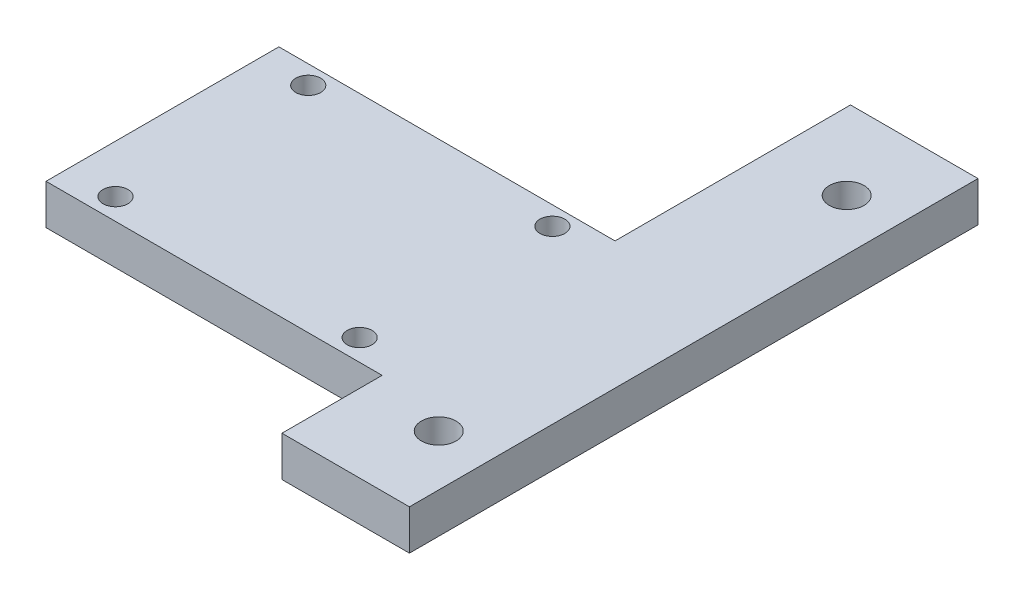
SolidWorks part; units mm, degrees
material "ABS"
ref_plane "Front Plane" through (0, 0, 0) normal (0, 0, 1) x (1, 0, 0)
ref_plane "Top Plane" through (0, 0, 0) normal (0, 1, 0) x (1, 0, 0)
ref_plane "Right Plane" through (0, 0, 0) normal (1, 0, 0) x (0, 0, -1)
sketch "Sketch1" plane through (0, 0, 0) normal (0, 1, 0) x (1, 0, 0)
  line L9 (6.0628, -8.2508) -> (36.55, -8.2508) construction
  line L16 (36.55, 27.1492) -> (36.55, -43.6508)
  line L17 (20.675, -43.6508) -> (36.55, -43.6508)
  line L18 (20.675, -31.174) -> (20.675, -43.6508)
  line L19 (20.675, -31.174) -> (-21.1827, -31.174)
  line L20 (-21.1827, -31.174) -> (-21.1827, -2.174)
  line L21 (-21.1827, -31.174) -> (20.675, -2.174) construction
  line L22 (-21.1827, -2.174) -> (20.675, -31.174) construction
  line L23 (-21.1827, -2.174) -> (20.675, -2.174)
  line L24 (6.0628, 14.5) -> (6.0628, -31.0016) construction
  line L25 (20.675, 27.1492) -> (36.55, 27.1492)
  line L26 (20.675, -2.174) -> (20.675, 27.1492)
  circle A6 centre (30.2, -33.6508) radius 2.159
  circle A7 centre (-15.2, -28.5016) radius 1.55
  circle A8 centre (15.2, -28.5016) radius 1.55
  circle A9 centre (-15.2, -4.5016) radius 1.55
  circle A10 centre (15.2, -4.5016) radius 1.55
  circle A11 centre (30.2, 17.1492) radius 2.159
  point P0 (0, 0)
  point P1 (0, 0)
  dimension "D3" = 4.318
  dimension "D4" = 10
  dimension "D5" = 15.875
  dimension "D2" = 4.318
  dimension "D1" = 10
  dimension "D6" = 15.875
  dimension "D7" = 41.8577
  dimension "D8" = 30.4
extrude "Boss-Extrude1" add sketch "Sketch1" along normal blind 5
